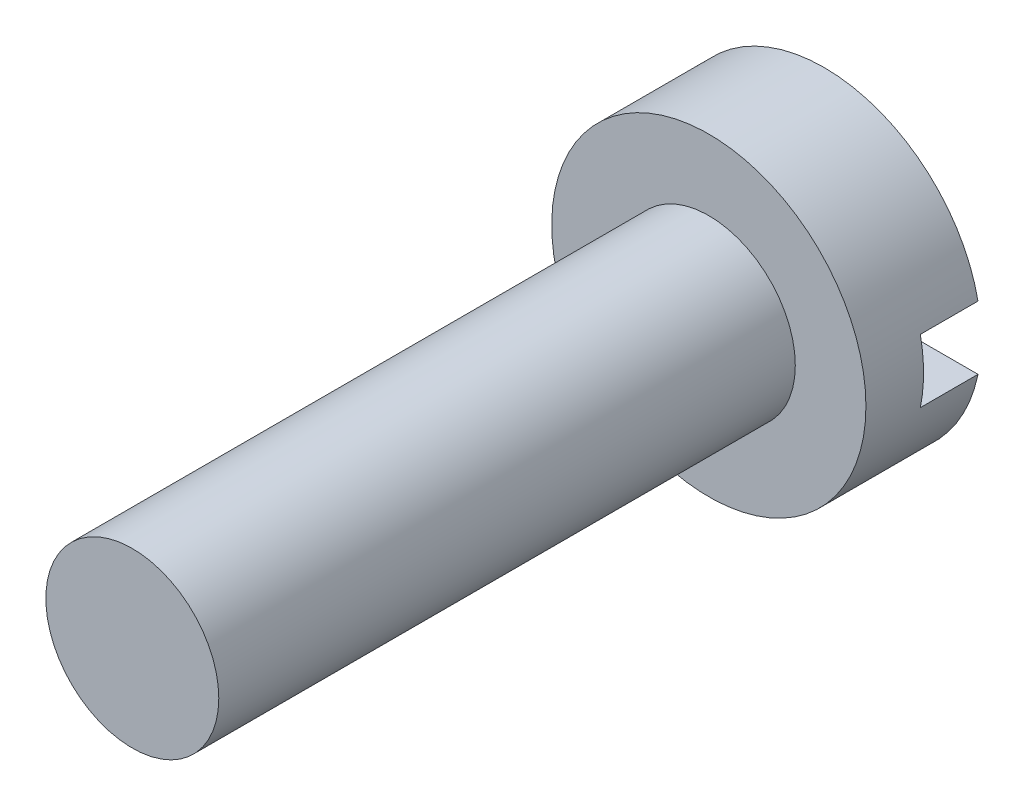
SolidWorks part; units mm, degrees
ref_plane "Front Plane" through (0, 0, 0) normal (0, 0, 1) x (1, 0, 0)
ref_plane "Top Plane" through (0, 0, 0) normal (0, 1, 0) x (1, 0, 0)
ref_plane "Right Plane" through (0, 0, 0) normal (1, 0, 0) x (0, 0, -1)
sketch "Sketch1" plane through (0, 0, 0) normal (0, 0, 1) x (1, 0, 0)
  circle A0 centre (0, 0) radius 2.725
extrude "Extrude1" add sketch "Sketch1" along normal blind 2
sketch "Sketch2" plane through (0, 0, 0) normal (0, 0, -1) x (-1, 0, 0)
  line L0 (-3.9013, 0) -> (3.4498, 0) construction
  line L1 (3.4498, 0) -> (3.4498, 0.55)
  line L2 (3.4498, 0.55) -> (-3.9013, 0.55)
  line L3 (-3.9013, 0.55) -> (-3.9013, -0.55)
  line L4 (-3.9013, -0.55) -> (3.4498, -0.55)
  line L5 (3.4498, -0.55) -> (3.4498, 0)
extrude "Cut-Extrude1" cut sketch "Sketch2" against normal blind 1
sketch "Sketch3" plane through (0, 0, 2) normal (0, 0, 1) x (1, 0, 0)
  circle A0 centre (0, 0) radius 1.5
extrude "Extrude2" add sketch "Sketch3" along normal blind 10
